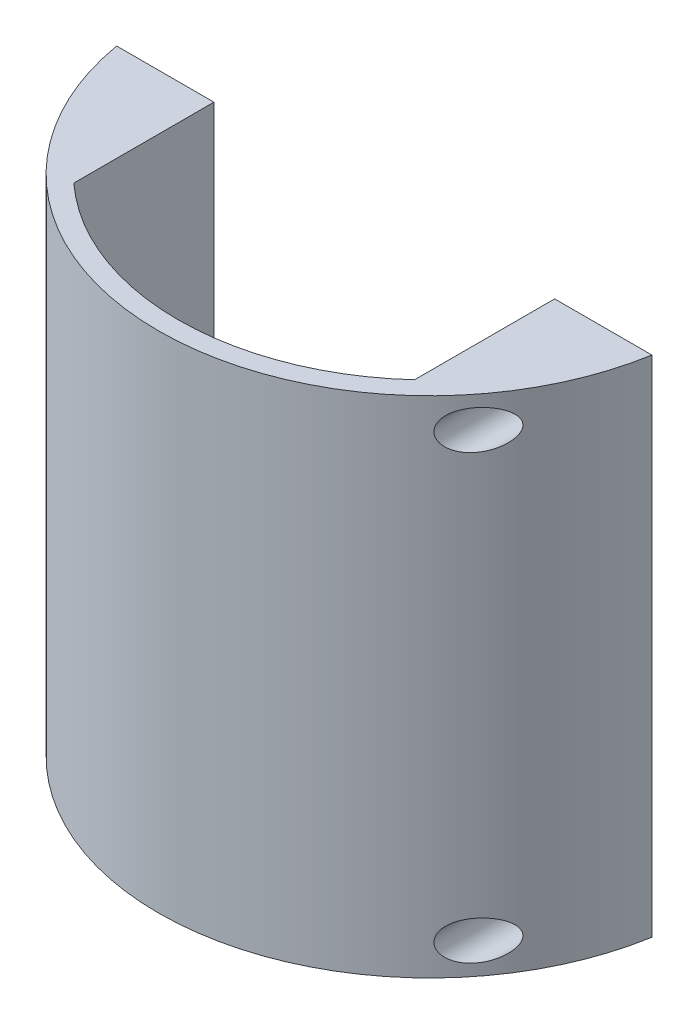
SolidWorks part; units mm, degrees
ref_plane "Front Plane" through (0, 0, 0) normal (0, 0, 1) x (1, 0, 0)
ref_plane "Top Plane" through (0, 0, 0) normal (0, 1, 0) x (1, 0, 0)
ref_plane "Right Plane" through (0, 0, 0) normal (1, 0, 0) x (0, 0, -1)
sketch "Sketch3" plane through (0, 0, 0) normal (0, 1, 0) x (1, 0, 0)
  line L0 (-43.815, -7.4865) -> (-40.5904, -7.4865)
  line L1 (40.5904, -7.4865) -> (43.815, -7.4865)
  arc A0 (-43.815, -7.4865) -> (43.815, -7.4865) centre (0, 0) ccw
  arc A1 (-40.5904, -7.4865) -> (40.5904, -7.4865) centre (0, 0) ccw
  dimension "D1" = 88.9
  dimension "D3" = 82.55
  dimension "D2" = 87.63
extrude "Boss-Extrude1" add sketch "Sketch3" along normal blind 82.55
sketch "Sketch4" plane through (0, 0, 7.4865) normal (0, 0, -1) x (-1, 0, 0)
  line L0 (0, 41.275) -> (43.815, 41.275) construction
  line L1 (-34.925, 5.08) -> (34.925, 5.08) construction
  line L2 (-34.925, 5.08) -> (-34.925, 77.47) construction
  line L3 (-34.925, 77.47) -> (34.925, 77.47) construction
  line L4 (34.925, 5.08) -> (34.925, 77.47) construction
  line L5 (-34.925, 5.08) -> (34.925, 77.47) construction
  line L6 (-34.925, 77.47) -> (34.925, 5.08) construction
  line L7 (43.815, 82.55) -> (43.815, 0) construction
  line L8 (40.5904, 82.55) -> (43.815, 82.55) construction
  line L9 (-27.8904, 0) -> (27.8904, 0)
  line L10 (-27.8904, 0) -> (-27.8904, 82.55)
  line L11 (-27.8904, 82.55) -> (27.8904, 82.55)
  line L12 (27.8904, 0) -> (27.8904, 82.55)
  line L13 (-27.8904, 0) -> (27.8904, 82.55) construction
  line L14 (-27.8904, 82.55) -> (27.8904, 0) construction
  line L15 (40.5904, 82.55) -> (40.5904, 0) construction
  line L16 (27.8904, 82.55) -> (40.5904, 82.55)
  line L17 (27.8904, 0) -> (40.5904, 0)
  line L18 (-40.5904, 82.55) -> (-27.8904, 82.55)
  line L19 (-40.5904, 0) -> (-27.8904, 0)
  line L20 (-40.5904, 82.55) -> (-40.5904, 0)
  line L21 (40.5904, 82.55) -> (40.5904, 0)
  circle A0 centre (34.925, 77.47) radius 3.175 construction
  circle A1 centre (34.925, 5.08) radius 3.175 construction
  circle A2 centre (-34.925, 77.47) radius 3.175 construction
  circle A3 centre (-34.925, 5.08) radius 3.175 construction
  point P0 (0, 41.275)
  line M12 (40.5904, 82.55) -> (40.5904, 0)
  dimension "D4" = 6.35
  dimension "D1" = 69.85
  dimension "D2" = 72.39
  dimension "D3" = 12.7
extrude "Boss-Extrude2" add sketch "Sketch4" against normal up to surface (22.9397 mm away) contours L18 L20 L19 L10 | L12 L17 L16 M12
sketch "Sketch5" plane through (0, 0, 7.4865) normal (0, 0, -1) x (-1, 0, 0)
  point P0 (-34.925, 77.47)
  point P3 (-34.925, 5.08)
  point P6 (34.925, 77.47)
  point P9 (34.925, 5.08)
hole_wizard "#6 Clearance Hole1" positions "Sketch5" profile "Sketch6" hole size "#6" standard "ANSI Inch" end condition through all
sketch "Sketch6" plane through (34.925, 77.47, 7.4865) normal (1, 0, 0) x (0, 1, 0)
  line L0 (0, 0) -> (0, 36.9635)
  line L1 (0, 36.9635) -> (1.8986, 36.9635)
  line L2 (1.8986, 36.9635) -> (1.8986, 0)
  line L5 (1.8986, 0) -> (0, 0)
  line L11 (0, -6.35) -> (0, 107.95) construction
  dimension "Thru Hole Dia." = 3.7973
  dimension "Thru Hole Depth" = 36.9635
ref_plane "Plane1" through (0, 0, 13.8365) normal (0, 0, -1) x (-1, 0, 0)
sketch "Sketch7" plane through (0, 0, 13.8365) normal (0, 0, -1) x (-1, 0, 0)
  circle A0 centre (-34.925, 5.08) radius 3.175 construction
  circle A1 centre (34.925, 5.08) radius 3.175 construction
  circle A2 centre (34.925, 77.47) radius 3.175 construction
  circle A3 centre (-34.925, 77.47) radius 3.175 construction
  circle A4 centre (-34.925, 5.08) radius 3.175
  circle A5 centre (34.925, 5.08) radius 3.175
  circle A6 centre (34.925, 77.47) radius 3.175
  circle A7 centre (-34.925, 77.47) radius 3.175
extrude "Cut-Extrude1" cut sketch "Sketch7" against normal through all
